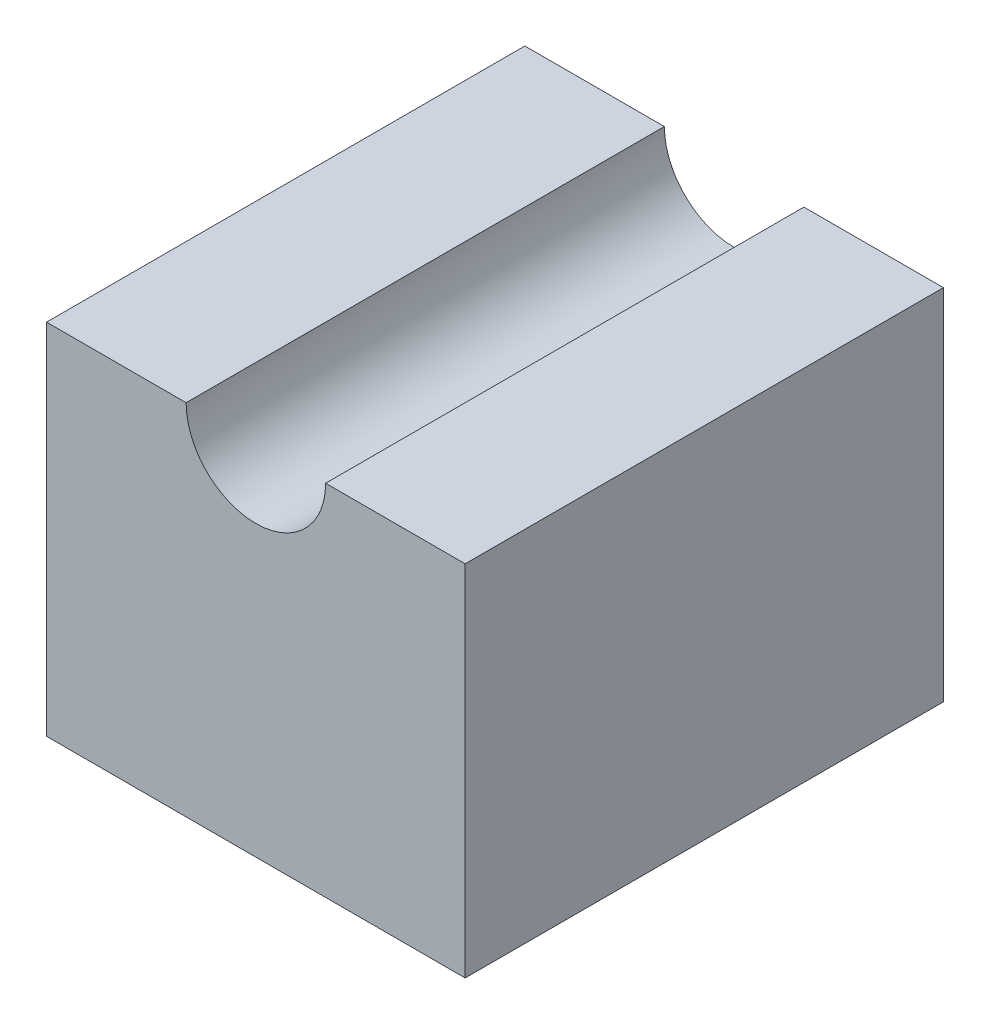
SolidWorks part; units mm, degrees
ref_plane "Front Plane" through (0, 0, 0) normal (0, 0, 1) x (1, 0, 0)
ref_plane "Top Plane" through (0, 0, 0) normal (0, 1, 0) x (1, 0, 0)
ref_plane "Right Plane" through (0, 0, 0) normal (1, 0, 0) x (0, 0, -1)
sketch "Sketch1" plane through (0, 0, 0) normal (0, 0, 1) x (1, 0, 0)
  line L0 (0, 0) -> (14.82, 0)
  line L1 (29.64, 0) -> (44.46, 0)
  line L2 (44.46, 0) -> (44.46, -38.1)
  line L3 (44.46, -38.1) -> (0, -38.1)
  line L4 (0, -38.1) -> (0, 0)
  arc A0 (14.82, 0) -> (29.64, 0) centre (22.23, 0) ccw
  dimension "D3" = 14.82
  dimension "D4" = 7.41
  dimension "D1" = 14.82
  dimension "D2" = 14.82
  dimension "D5" = 38.1
extrude "Boss-Extrude1" add sketch "Sketch1" along normal blind 50.8
